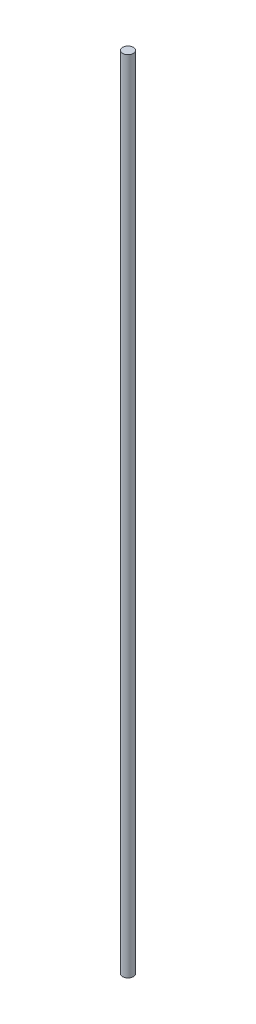
SolidWorks part; units mm, degrees
ref_plane "Front Plane" through (0, 0, 0) normal (0, 0, 1) x (1, 0, 0)
ref_plane "Top Plane" through (0, 0, 0) normal (0, 1, 0) x (1, 0, 0)
ref_plane "Right Plane" through (0, 0, 0) normal (1, 0, 0) x (0, 0, -1)
sketch "Sketch2" plane through (0, 0, 0) normal (0, 1, 0) x (1, 0, 0)
  circle A0 centre (0, 0) radius 10
extrude "Boss-Extrude1" add sketch "Sketch2" along normal blind 1500
